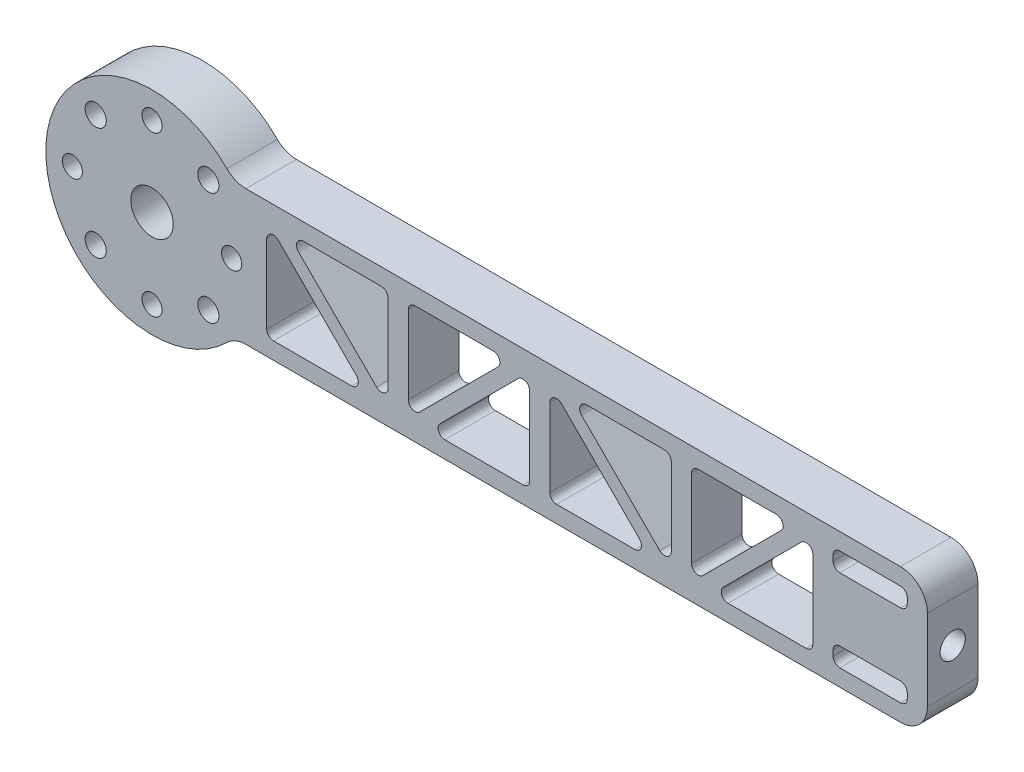
SolidWorks part; units mm, degrees
ref_plane "Front Plane" through (0, 0, 0) normal (0, 0, 1) x (1, 0, 0)
ref_plane "Top Plane" through (0, 0, 0) normal (0, 1, 0) x (1, 0, 0)
ref_plane "Right Plane" through (0, 0, 0) normal (1, 0, 0) x (0, 0, -1)
sketch "Sketch1" plane through (0, 0, 0) normal (0, 0, 1) x (1, 0, 0)
  line L0 (0, -1000) -> (0, 49000) construction
  line L1 (73.025, 12.7) -> (73.025, -12.7)
  line L2 (-73.025, 0) -> (-73.025, -12.7) construction
  line L5 (-73.025, 20) -> (73.025, -20) construction
  line L6 (-73.025, -20) -> (73.025, 20) construction
  line L7 (-1000, 0) -> (49000, 0) construction
  line L8 (-73.025, 0) -> (-73.025, 12.7) construction
  line L9 (-57.5748, 12.7) -> (73.025, 12.7)
  line L10 (-57.5748, -12.7) -> (73.025, -12.7)
  arc A0 (-73.025, 20) -> (-73.025, -20) centre (-73.025, 0) ccw
  circle A1 centre (-73.025, 0) radius 4
  arc A2 (-73.025, 20) -> (-57.5748, 12.7) centre (-73.025, 0) cw
  arc A3 (-57.5748, -12.7) -> (-73.025, -20) centre (-73.025, 0) cw
  point P0 (0, 0)
  dimension "D3" = 8
  dimension "D4" = 12.7
  dimension "D1" = 146.05
  dimension "D2" = 40
  dimension "D5" = 12.7
extrude "Boss-Extrude1" add sketch "Sketch1" along normal blind 9.525
sketch "Sketch3" plane through (0, 0, 0) normal (0, 0, 1) x (1, 0, 0)
  line L0 (-73.025, 0) -> (-83.6316, -10.6066) construction
  line L1 (-1047.73, 0) -> (48952.27, 0) construction
  line L2 (-73.025, 0) -> (-73.025, 15) construction
  circle A0 centre (-73.025, 0) radius 15 construction
  circle A1 centre (-73.025, 15) radius 1.8987
  circle A2 centre (-58.025, 0) radius 1.8986
  circle A3 centre (-73.025, -15) radius 1.8987
  circle A4 centre (-88.025, 0) radius 1.8987
  circle A5 centre (-83.6316, -10.6066) radius 1.9939
  circle A6 centre (-83.6316, 10.6066) radius 1.9939
  circle A7 centre (-62.4184, 10.6066) radius 1.9939
  circle A8 centre (-62.4184, -10.6066) radius 1.9939
  point P23 (-73.025, 0)
  point P25 (-73.025, 0)
  dimension "D1" = 30
  dimension "D2" = 3.7973
  dimension "D4" = 45
  dimension "D5" = 3.9878
  dimension "D6" = 4
  dimension "D3" = 4
extrude "Cut-Extrude2" cut sketch "Sketch3" along normal through all
sketch "Sketch19" plane through (0, 0, 9.525) normal (0, 0, 1) x (1, 0, 0)
  line L1 (-51.4245, -9.525) -> (-32.3745, -9.525)
  line L2 (55.2555, 9.525) -> (69.2255, 9.525)
  line L4 (-51.4245, -9.525) -> (-51.4245, 9.525)
  line L8 (-51.4245, 9.525) -> (-32.3745, -9.525)
  line L9 (-1.8945, 9.525) -> (0.0105, 9.525) construction
  line L10 (69.2255, 9.525) -> (69.2255, 5.969)
  line L15 (67.9485, 0) -> (57.7885, 0) construction
  line L16 (-51.4245, 9.525) -> (-47.6145, 9.525) construction
  line L17 (-32.3745, -9.525) -> (-28.5645, -9.525) construction
  line L18 (-47.6145, 9.525) -> (-28.5645, -9.525)
  line L19 (-28.5645, -9.525) -> (-28.5645, 9.525)
  line L20 (-28.5645, 9.525) -> (-47.6145, 9.525)
  line L21 (-28.5645, 9.525) -> (-26.6595, 9.525) construction
  line L22 (-26.6595, 9.525) -> (-26.6595, -9.525) construction
  line L23 (-1.8945, -9.525) -> (-20.9445, -9.525)
  line L24 (-1.8945, -9.525) -> (-1.8945, 9.525)
  line L25 (-1.8945, 9.525) -> (-20.9445, -9.525)
  line L26 (-24.7545, -9.525) -> (-24.7545, 9.525)
  line L27 (-5.7045, 9.525) -> (-24.7545, -9.525)
  line L28 (-24.7545, 9.525) -> (-5.7045, 9.525)
  line L29 (0.0105, 9.525) -> (0.0105, -9.525) construction
  line L30 (1.9155, -9.525) -> (1.9155, 9.525)
  line L31 (1.9155, 9.525) -> (20.9655, -9.525)
  line L32 (1.9155, -9.525) -> (20.9655, -9.525)
  line L33 (5.7255, 9.525) -> (24.7755, -9.525)
  line L34 (24.7755, 9.525) -> (5.7255, 9.525)
  line L35 (24.7755, -9.525) -> (24.7755, 9.525)
  line L36 (24.7755, 9.525) -> (26.6805, 9.525) construction
  line L37 (26.6805, 9.525) -> (26.6805, -9.525) construction
  line L38 (28.5855, 9.525) -> (47.6355, 9.525)
  line L39 (28.5855, -9.525) -> (28.5855, 9.525)
  line L40 (47.6355, 9.525) -> (28.5855, -9.525)
  line L41 (51.4455, -9.525) -> (32.3955, -9.525)
  line L42 (51.4455, 9.525) -> (32.3955, -9.525)
  line L43 (51.4455, -9.525) -> (51.4455, 9.525)
  line L44 (51.4455, 9.525) -> (55.2555, 9.525) construction
  line L45 (55.2555, 9.525) -> (55.2555, 5.969)
  line L46 (69.2255, 5.969) -> (55.2555, 5.969)
  line L47 (69.2255, -9.525) -> (69.2255, -5.969)
  line L48 (55.2555, -9.525) -> (69.2255, -9.525)
  line L49 (55.2555, -9.525) -> (55.2555, -5.969)
  line L50 (69.2255, -5.969) -> (55.2555, -5.969)
  point P6 (8.262, 0)
  dimension "D1" = 19.05
  dimension "D2" = 19.05
  dimension "D3" = 10.16
  dimension "D4" = 3.81
  dimension "D5" = 3.81
  dimension "D6" = 1.905
  dimension "D7" = 1.905
  dimension "D8" = 1.905
  dimension "D9" = 3.81
  dimension "D10" = 13.97
  dimension "D11" = 3.556
extrude "Cut-Extrude4" cut sketch "Sketch19" against normal through all
sketch "Sketch20" plane through (73.025, 0, 0) normal (1, 0, 0) x (0, 0, -1)
  line L0 (-9.525, 12.7) -> (0, -12.7) construction
  circle A0 centre (-4.7625, 0) radius 2.3813
  dimension "D1" = 4.7625
extrude "Cut-Extrude5" cut sketch "Sketch20" against normal up to next
fillet "Fillet5" radius 5.08 2 edges at (73.025, -12.7, 4.7625) (73.025, 12.7, 4.7625)
fillet "Fillet6" radius 5.08 2 edges at (-57.5748, -12.7, 4.7625) (-57.5748, 12.7, 4.7625)
fillet "Fillet7" radius 1.27 32 edges at (51.4455, 9.525, 4.7625) (51.4455, -9.525, 4.7625) (32.3955, -9.525, 4.7625) (47.6355, 9.525, 4.7625) (28.5855, -9.525, 4.7625) (28.5855, 9.525, 4.7625) (5.7255, 9.525, 4.7625) (24.7755, -9.525, 4.7625) (24.7755, 9.525, 4.7625) (20.9655, -9.525, 4.7625) (1.9155, -9.525, 4.7625) (1.9155, 9.525, 4.7625) (-1.8945, 9.525, 4.7625) (-1.8945, -9.525, 4.7625) (-20.9445, -9.525, 4.7625) (-24.7545, -9.525, 4.7625) (-24.7545, 9.525, 4.7625) (-5.7045, 9.525, 4.7625) (-28.5645, 9.525, 4.7625) (-28.5645, -9.525, 4.7625) (-47.6145, 9.525, 4.7625) (-51.4245, 9.525, 4.7625) (-32.3745, -9.525, 4.7625) (-51.4245, -9.525, 4.7625) (69.2255, 9.525, 4.7625) (69.2255, 5.969, 4.7625) (55.2555, 9.525, 4.7625) (55.2555, 5.969, 4.7625) (55.2555, -5.969, 4.7625) (55.2555, -9.525, 4.7625) (69.2255, -9.525, 4.7625) (69.2255, -5.969, 4.7625)
